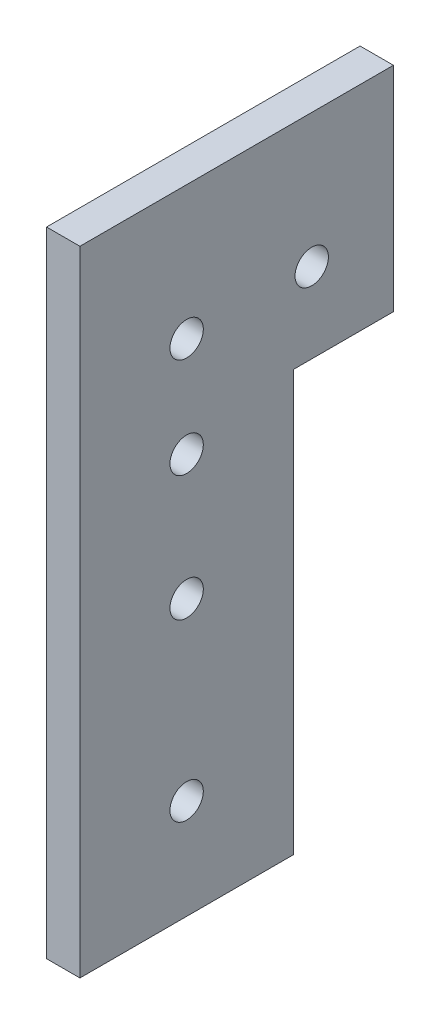
SolidWorks part; units mm, degrees
ref_plane "Front Plane" through (0, 0, 0) normal (0, 0, 1) x (1, 0, 0)
ref_plane "Top Plane" through (0, 0, 0) normal (0, 1, 0) x (1, 0, 0)
ref_plane "Right Plane" through (0, 0, 0) normal (1, 0, 0) x (0, 0, -1)
sketch "Sketch1" plane through (0, 0, 0) normal (1, 0, 0) x (0, 0, -1)
  line L1 (0, 0) -> (40.64, 0)
  line L2 (0, 0) -> (0, 120.65)
  line L3 (0, 120.65) -> (40.64, 120.65)
  line L4 (40.64, 0) -> (40.64, 80.01)
  line L5 (40.64, 120.65) -> (59.69, 120.65)
  line L7 (40.64, 80.01) -> (59.69, 80.01)
  line L8 (59.69, 120.65) -> (59.69, 80.01)
  dimension "D1" = 40.64
  dimension "D2" = 120.65
  dimension "D3" = 19.05
  dimension "D4" = 40.64
extrude "Boss-Extrude1" add sketch "Sketch1" along normal blind 6.35
sketch "Sketch3" plane through (6.35, 0, 0) normal (1, 0, 0) x (0, 0, -1)
  line L0 (59.69, 120.65) -> (0, 120.65) construction
  line L1 (0, 120.65) -> (0, 0) construction
  circle A0 centre (20.32, 19.05) radius 3.175
  circle A1 centre (20.32, 52.3875) radius 3.175
  circle A2 centre (20.32, 76.2) radius 3.175
  circle A3 centre (20.32, 95.25) radius 3.175
  circle A4 centre (44.1325, 95.25) radius 3.175
  dimension "D1" = 33.3375
  dimension "D2" = 23.8125
  dimension "D4" = 25.4
  dimension "D5" = 20.32
  dimension "D6" = 6.35
  dimension "D7" = 23.8125
  dimension "D3" = 19.05
extrude "Cut-Extrude1" cut sketch "Sketch3" against normal blind 6.35
